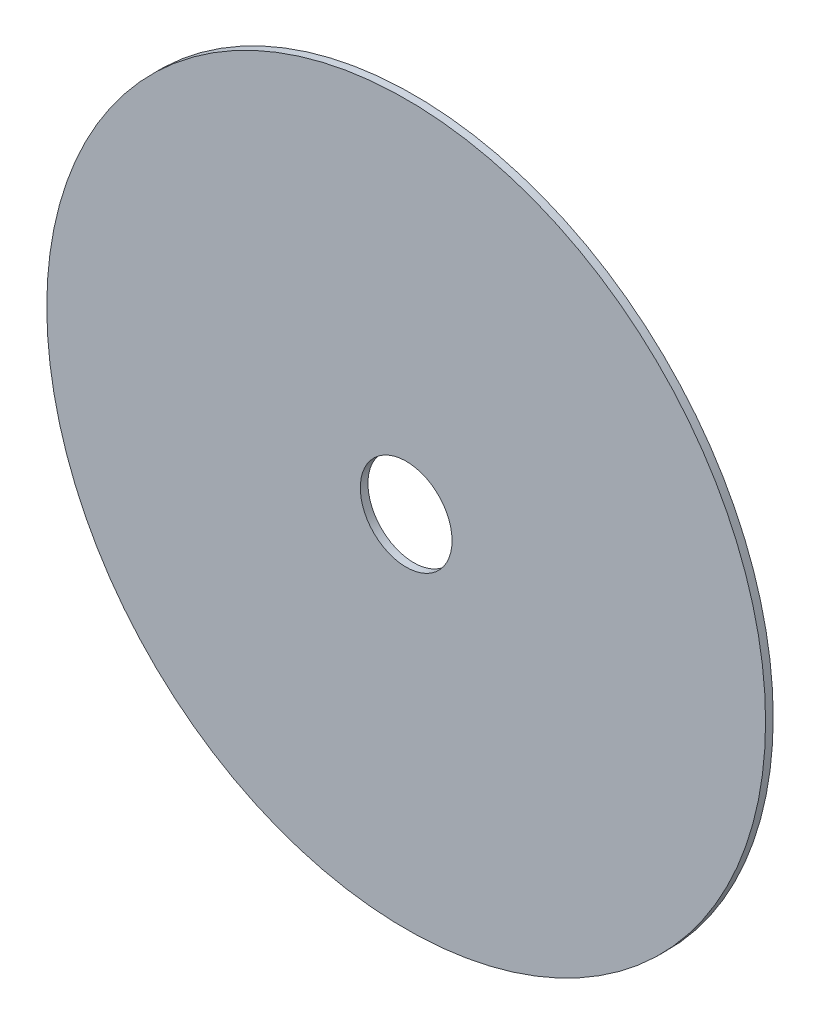
SolidWorks part; units mm, degrees
material "PC High Viscosity"
ref_plane "Front" through (0, 0, 0) normal (0, 0, 1) x (1, 0, 0)
ref_plane "Top" through (0, 0, 0) normal (0, 1, 0) x (1, 0, 0)
ref_plane "Right" through (0, 0, 0) normal (1, 0, 0) x (0, 0, -1)
sketch "Sketch1" plane through (0, 0, 0) normal (0, 0, 1) x (1, 0, 0)
  circle A0 centre (0, 0) radius 59.69
  circle A1 centre (0, 0) radius 7.62
  dimension "D1" = 119.38
  dimension "D2" = 15.24
extrude "Boss-Extrude1" add sketch "Sketch1" along normal blind 1.27
